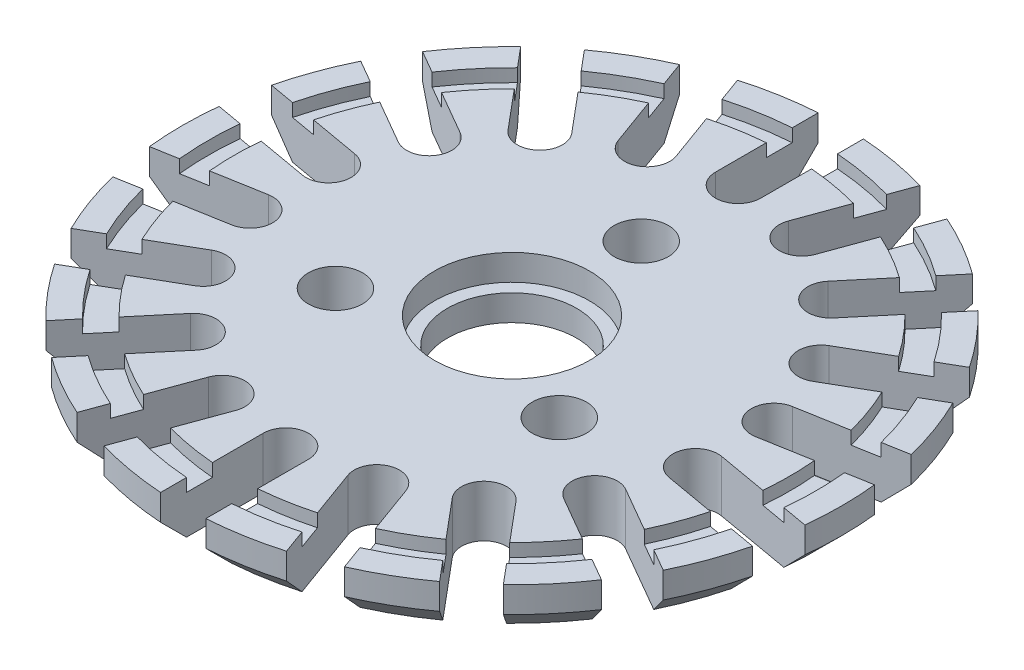
SolidWorks part; units mm, degrees
material "Liga 1060"
ref_plane "Plano frontal" through (0, 0, 0) normal (0, 0, 1) x (1, 0, 0)
ref_plane "Plano superior" through (0, 0, 0) normal (0, 1, 0) x (1, 0, 0)
ref_plane "Plano direito" through (0, 0, 0) normal (1, 0, 0) x (0, 0, -1)
sketch "Esboço1" plane through (0, 0, 0) normal (0, 1, 0) x (1, 0, 0)
  line L0 (1.75, 17.5) -> (1.75, 25.4399)
  line L1 (-1.75, 17.5) -> (-1.75, 25.4399)
  line L2 (4.3409, 17.0432) -> (7.0565, 24.5042)
  line L3 (7.6298, 15.8461) -> (10.3454, 23.3071)
  line L4 (9.9082, 14.5307) -> (15.0119, 20.613)
  line L5 (12.5894, 12.2809) -> (17.693, 18.3632)
  line L6 (14.2804, 10.2655) -> (21.1566, 14.2355)
  line L7 (16.0304, 7.2345) -> (22.9066, 11.2044)
  line L8 (16.9303, 4.7623) -> (24.7495, 6.141)
  line L9 (17.538, 1.3154) -> (25.3573, 2.6942)
  line L10 (17.538, -1.3154) -> (25.3573, -2.6942)
  line L11 (16.9303, -4.7623) -> (24.7495, -6.141)
  line L12 (16.0304, -7.2345) -> (22.9066, -11.2044)
  line L13 (14.2804, -10.2655) -> (21.1566, -14.2355)
  line L14 (12.5894, -12.2809) -> (17.693, -18.3632)
  line L15 (9.9082, -14.5307) -> (15.0119, -20.613)
  line L16 (7.6298, -15.8461) -> (10.3454, -23.3071)
  line L17 (4.3409, -17.0432) -> (7.0565, -24.5042)
  line L18 (1.75, -17.5) -> (1.75, -25.4399)
  line L19 (-1.75, -17.5) -> (-1.75, -25.4399)
  line L20 (-4.3409, -17.0432) -> (-7.0565, -24.5042)
  line L21 (-7.6298, -15.8461) -> (-10.3454, -23.3071)
  line L22 (-9.9082, -14.5307) -> (-15.0119, -20.613)
  line L23 (-12.5894, -12.2809) -> (-17.693, -18.3632)
  line L24 (-14.2804, -10.2655) -> (-21.1566, -14.2355)
  line L25 (-16.0304, -7.2345) -> (-22.9066, -11.2044)
  line L26 (-16.9303, -4.7623) -> (-24.7495, -6.141)
  line L27 (-17.538, -1.3154) -> (-25.3573, -2.6942)
  line L28 (-17.538, 1.3154) -> (-25.3573, 2.6942)
  line L29 (-16.9303, 4.7623) -> (-24.7495, 6.141)
  line L30 (-16.0304, 7.2345) -> (-22.9066, 11.2044)
  line L31 (-14.2804, 10.2655) -> (-21.1566, 14.2355)
  line L32 (-12.5894, 12.2809) -> (-17.693, 18.3632)
  line L33 (-9.9082, 14.5307) -> (-15.0119, 20.613)
  line L34 (-7.6298, 15.8461) -> (-10.3454, 23.3071)
  line L35 (-4.3409, 17.0432) -> (-7.0565, 24.5042)
  arc A0 (-1.75, 25.4399) -> (-7.0565, 24.5042) centre (0, 0) ccw
  circle A1 centre (0, 0) radius 5
  circle A2 centre (0, 0) radius 17.5 construction
  arc A3 (-1.75, 17.5) -> (1.75, 17.5) centre (0, 17.5) ccw
  arc A4 (4.3409, 17.0432) -> (7.6298, 15.8461) centre (5.9854, 16.4446) ccw
  arc A5 (9.9082, 14.5307) -> (12.5894, 12.2809) centre (11.2488, 13.4058) ccw
  arc A6 (14.2804, 10.2655) -> (16.0304, 7.2345) centre (15.1554, 8.75) ccw
  arc A7 (16.9303, 4.7623) -> (17.538, 1.3154) centre (17.2341, 3.0388) ccw
  arc A8 (17.538, -1.3154) -> (16.9303, -4.7623) centre (17.2341, -3.0388) ccw
  arc A9 (16.0304, -7.2345) -> (14.2804, -10.2655) centre (15.1554, -8.75) ccw
  arc A10 (12.5894, -12.2809) -> (9.9082, -14.5307) centre (11.2488, -13.4058) ccw
  arc A11 (7.6298, -15.8461) -> (4.3409, -17.0432) centre (5.9854, -16.4446) ccw
  arc A12 (1.75, -17.5) -> (-1.75, -17.5) centre (0, -17.5) ccw
  arc A13 (-4.3409, -17.0432) -> (-7.6298, -15.8461) centre (-5.9854, -16.4446) ccw
  arc A14 (-9.9082, -14.5307) -> (-12.5894, -12.2809) centre (-11.2488, -13.4058) ccw
  arc A15 (-14.2804, -10.2655) -> (-16.0304, -7.2345) centre (-15.1554, -8.75) ccw
  arc A16 (-16.9303, -4.7623) -> (-17.538, -1.3154) centre (-17.2341, -3.0388) ccw
  arc A17 (-17.538, 1.3154) -> (-16.9303, 4.7623) centre (-17.2341, 3.0388) ccw
  arc A18 (-16.0304, 7.2345) -> (-14.2804, 10.2655) centre (-15.1554, 8.75) ccw
  arc A19 (-12.5894, 12.2809) -> (-9.9082, 14.5307) centre (-11.2488, 13.4058) ccw
  arc A20 (-7.6298, 15.8461) -> (-4.3409, 17.0432) centre (-5.9854, 16.4446) ccw
  arc A21 (-10.3454, 23.3071) -> (-15.0119, 20.613) centre (0, 0) ccw
  arc A22 (7.0565, 24.5042) -> (1.75, 25.4399) centre (0, 0) ccw
  arc A23 (-17.693, 18.3632) -> (-21.1566, 14.2355) centre (0, 0) ccw
  arc A24 (-22.9066, 11.2044) -> (-24.7495, 6.141) centre (0, 0) ccw
  arc A25 (-25.3573, 2.6942) -> (-25.3573, -2.6942) centre (0, 0) ccw
  arc A26 (-24.7495, -6.141) -> (-22.9066, -11.2044) centre (0, 0) ccw
  arc A27 (-21.1566, -14.2355) -> (-17.693, -18.3632) centre (0, 0) ccw
  arc A28 (-15.0119, -20.613) -> (-10.3454, -23.3071) centre (0, 0) ccw
  arc A29 (-7.0565, -24.5042) -> (-1.75, -25.4399) centre (0, 0) ccw
  arc A30 (1.75, -25.4399) -> (7.0565, -24.5042) centre (0, 0) ccw
  arc A31 (10.3454, -23.3071) -> (15.0119, -20.613) centre (0, 0) ccw
  arc A32 (17.693, -18.3632) -> (21.1566, -14.2355) centre (0, 0) ccw
  arc A33 (22.9066, -11.2044) -> (24.7495, -6.141) centre (0, 0) ccw
  arc A34 (25.3573, -2.6942) -> (25.3573, 2.6942) centre (0, 0) ccw
  arc A35 (24.7495, 6.141) -> (22.9066, 11.2044) centre (0, 0) ccw
  arc A36 (21.1566, 14.2355) -> (17.693, 18.3632) centre (0, 0) ccw
  arc A37 (15.0119, 20.613) -> (10.3454, 23.3071) centre (0, 0) ccw
  dimension "D1" = 51
  dimension "D2" = 10
  dimension "D3" = 35
  dimension "D4" = 3.5
  dimension "D5" = 7.9399
extrude "Ressalto-extrusão1" add sketch "Esboço1" along normal blind 4
sketch "Esboço2" plane through (0, 4, 0) normal (0, 1, 0) x (1, 0, 0)
  circle A0 centre (0, 0) radius 6
  dimension "D1" = 12
extrude "Corte-extrusão1" cut sketch "Esboço2" against normal blind 2
sketch "Esboço3" plane through (0, 4, 0) normal (0, 1, 0) x (1, 0, 0)
  circle A0 centre (0, 0) radius 23.5
  circle A1 centre (0, 0) radius 21.5
  dimension "D1" = 47
  dimension "D2" = 43
extrude "Corte-extrusão2" cut sketch "Esboço3" against normal blind 1
chamfer "Chanfro1" distance 2 angle 45 18 edges at (25.5, 0, 0) (23.9622, 0, 8.7215) (19.5341, 0, 16.3911) (12.75, 0, 22.0836) (4.428, 0, 25.1126) (-4.428, 0, 25.1126) (-12.75, 0, 22.0836) (-19.5341, 0, 16.3911) (-23.9622, 0, 8.7215) (-25.5, 0, 0) (-23.9622, 0, -8.7215) (-19.5341, 0, -16.3911) (-12.75, 0, -22.0836) (-4.428, 0, -25.1126) (4.428, 0, -25.1126) (12.75, 0, -22.0836) (19.5341, 0, -16.3911) (23.9622, 0, -8.7215)
sketch "Esboço4" plane through (0, 0, 0) normal (0, -1, 0) x (1, 0, 0)
  line L0 (0, -10) -> (0, 10) construction
  circle A0 centre (0, 0) radius 10 construction
  circle A1 centre (0, -10) radius 2.095
  circle A2 centre (-8.6603, 5) radius 2.095
  circle A3 centre (8.6603, 5) radius 2.095
  dimension "D1" = 20
  dimension "D2" = 4.19
  dimension "D4" = 10
  dimension "D5" = 10
  dimension "D6" = 20
  dimension "D3" = 3
extrude "Corte-extrusão3" cut sketch "Esboço4" against normal through all
sketch "Esboço5" plane through (0, 0, 0) normal (0, -1, 0) x (1, 0, 0)
  line L0 (0, 0) -> (8.6603, 5) construction
  line L1 (0, 0) -> (-8.6603, 5) construction
  line L2 (0, 0) -> (0, -10) construction
  line L4 (11.4303, 5) -> (10.0453, 7.3989)
  line L5 (10.0453, 7.3989) -> (7.2753, 7.3989)
  line L6 (7.2753, 7.3989) -> (5.8903, 5)
  line L7 (5.8903, 5) -> (7.2753, 2.6011)
  line L8 (7.2753, 2.6011) -> (10.0453, 2.6011)
  line L9 (10.0453, 2.6011) -> (11.4303, 5)
  line L10 (-5.8903, 5) -> (-7.2753, 7.3989)
  line L11 (-7.2753, 7.3989) -> (-10.0453, 7.3989)
  line L12 (-10.0453, 7.3989) -> (-11.4303, 5)
  line L13 (-11.4303, 5) -> (-10.0453, 2.6011)
  line L14 (-10.0453, 2.6011) -> (-7.2753, 2.6011)
  line L15 (-7.2753, 2.6011) -> (-5.8903, 5)
  line L16 (2.77, -10) -> (1.385, -7.6011)
  line L17 (1.385, -7.6011) -> (-1.385, -7.6011)
  line L18 (-1.385, -7.6011) -> (-2.77, -10)
  line L19 (-2.77, -10) -> (-1.385, -12.3989)
  line L20 (-1.385, -12.3989) -> (1.385, -12.3989)
  line L21 (1.385, -12.3989) -> (2.77, -10)
  circle A0 centre (8.6603, 5) radius 2.3989 construction
  circle A1 centre (-8.6603, 5) radius 2.3989 construction
  circle A2 centre (0, -10) radius 2.3989 construction
  dimension "D1" = 2.77
extrude "Corte-extrusão4" cut sketch "Esboço5" against normal blind 0.42
